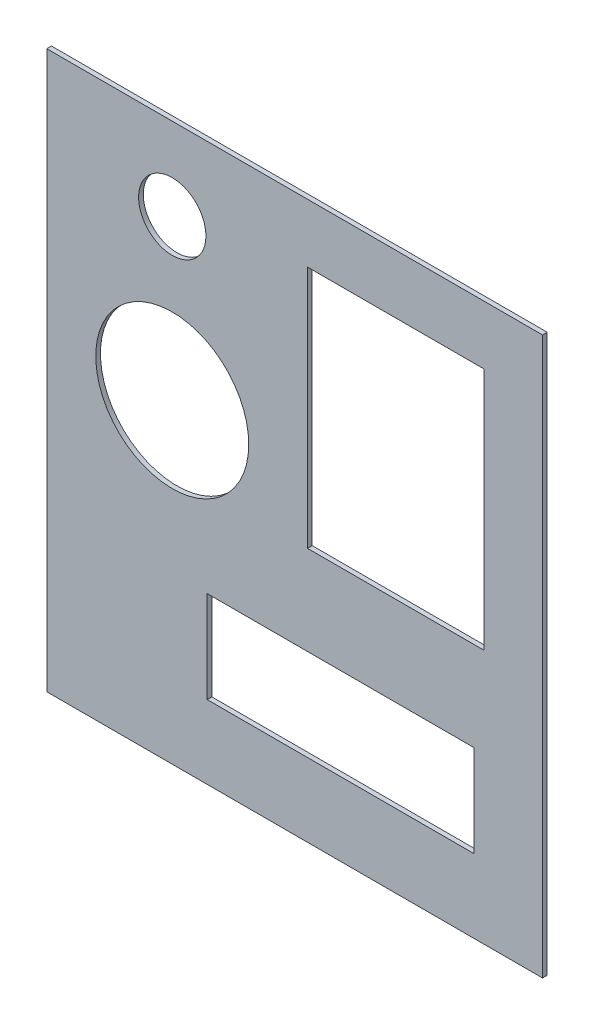
SolidWorks part; units mm, degrees
ref_plane "Front Plane" through (0, 0, 0) normal (0, 0, 1) x (1, 0, 0)
ref_plane "Top Plane" through (0, 0, 0) normal (0, 1, 0) x (1, 0, 0)
ref_plane "Right Plane" through (0, 0, 0) normal (1, 0, 0) x (0, 0, -1)
sketch "Sketch1" plane through (0, 0, 0) normal (0, 0, 1) x (1, 0, 0)
  line L1 (-64.2937, -72.2313) -> (64.2938, -72.2313)
  line L2 (-64.2937, -72.2313) -> (-64.2937, 72.2313)
  line L3 (-64.2937, 72.2313) -> (64.2938, 72.2313)
  line L4 (64.2938, -72.2313) -> (64.2938, 72.2313)
  line L5 (-64.2937, -72.2313) -> (64.2938, 72.2313) construction
  line L6 (-64.2937, 72.2313) -> (64.2938, -72.2313) construction
  point P0 (0, 0)
  dimension "D1" = 128.5875
  dimension "D2" = 144.4625
extrude "Boss-Extrude1" add sketch "Sketch1" along normal blind 1.2141 contours L3 L4 L1 L2
sketch "Sketch3" plane through (0, 0, 1.2141) normal (0, 0, 1) x (1, 0, 0)
  line L0 (-64.2937, 72.2313) -> (64.2938, 72.2313) construction
  line L1 (-27.7812, -59.5312) -> (51.5938, -59.5312)
  line L2 (-27.7812, -59.5312) -> (-27.7812, -23.0187)
  line L3 (-27.7812, -23.0187) -> (51.5938, -23.0187)
  line L4 (51.5938, -59.5312) -> (51.5938, -23.0187)
  line L5 (-27.7812, -59.5312) -> (51.5938, -23.0187) construction
  line L6 (-27.7812, -23.0187) -> (51.5938, -59.5312) construction
  line L7 (0.7938, -8.7313) -> (51.5938, -8.7313)
  line L8 (0.7938, -8.7313) -> (0.7938, 59.5312)
  line L9 (0.7938, 59.5312) -> (51.5938, 59.5312)
  line L10 (51.5938, -8.7313) -> (51.5938, 59.5312)
  line L11 (0.7938, -8.7313) -> (51.5938, 59.5312) construction
  line L12 (0.7938, 59.5312) -> (51.5938, -8.7313) construction
  line L13 (-64.2937, -72.2313) -> (64.2938, -72.2313) construction
  line L14 (64.2938, -72.2313) -> (64.2938, 72.2313) construction
  circle A0 centre (-31.75, 50.8) radius 8.7313
  circle A1 centre (-31.75, 9.525) radius 19.8438
  point P4 (11.9063, -41.275)
  point P9 (26.1938, 25.4)
  dimension "D1" = 79.375
  dimension "D5" = 17.4625
  dimension "D6" = 39.6875
  dimension "D11" = 32.5437
  dimension "D2" = 36.5125
  dimension "D3" = 50.8
  dimension "D4" = 68.2625
  dimension "D7" = 12.7
  dimension "D8" = 12.7
  dimension "D9" = 12.7
  dimension "D10" = 12.7
  dimension "D12" = 41.275
  dimension "D13" = 32.5437
extrude "Cut-Extrude1" cut sketch "Sketch3" against normal through all
sketch "Sketch4" plane through (0, 0, 1.2141) normal (0, 0, 1) x (1, 0, 0)
  line L10 (0.7938, -8.7313) -> (51.5938, -8.7313) construction
  line L11 (51.5938, -8.7313) -> (51.5938, 59.5312) construction
  line L12 (51.5938, 59.5312) -> (0.7938, 59.5312) construction
  line L13 (0.7938, 59.5312) -> (0.7938, -8.7313) construction
  line L14 (3.3338, -6.1913) -> (49.0538, -6.1913)
  line L15 (49.0538, -6.1913) -> (49.0538, 56.9912)
  line L16 (3.3338, 56.9912) -> (3.3338, -6.1913)
  line L17 (49.0538, 56.9912) -> (3.3338, 56.9912)
  line L18 (3.3338, -6.1913) -> (49.0538, -6.1913)
  line L19 (49.0538, -6.1913) -> (49.0538, 56.9912)
  line L20 (3.3338, 56.9912) -> (3.3338, -6.1913)
  line L21 (49.0538, 56.9912) -> (3.3338, 56.9912)
  line L22 (0.7938, -8.7313) -> (51.5938, -8.7313)
  line L23 (51.5938, -8.7313) -> (51.5938, 59.5312)
  line L24 (51.5938, 59.5312) -> (0.7938, 59.5312)
  line L25 (0.7938, 59.5312) -> (0.7938, -8.7313)
  dimension "D1" = 2.54
extrude "Boss-Extrude2" add sketch "Sketch4" against normal up to surface (1.2141 mm away) up to face at (-11.9062, 9.525, 0)
sketch "Sketch5" plane through (0, 0, 1.2141) normal (0, 0, 1) x (1, 0, 0)
  line L0 (51.5938, -59.5312) -> (51.5938, -23.0187) construction
  line L1 (-27.7812, -59.5312) -> (51.5938, -59.5312) construction
  line L2 (-27.7812, -23.0187) -> (-27.7812, -59.5312) construction
  line L3 (51.5938, -23.0187) -> (-27.7812, -23.0187) construction
  line L4 (51.5938, -59.5312) -> (51.5938, -23.0187)
  line L5 (-27.7812, -59.5312) -> (51.5938, -59.5312)
  line L6 (-27.7812, -23.0187) -> (-27.7812, -59.5312)
  line L7 (51.5938, -23.0187) -> (-27.7812, -23.0187)
  line L8 (46.5138, -29.3687) -> (-22.7012, -29.3687)
  line L9 (-22.7012, -53.1812) -> (46.5138, -53.1812)
  line L10 (-22.7012, -29.3687) -> (-22.7012, -53.1812)
  line L11 (46.5138, -53.1812) -> (46.5138, -29.3687)
  line L12 (-22.7012, -23.0187) -> (-22.7012, -59.5312) construction
  line L13 (51.5938, -29.3687) -> (-27.7812, -29.3687) construction
  line L14 (-27.7812, -53.1812) -> (51.5938, -53.1812) construction
  line L15 (46.5138, -59.5312) -> (46.5138, -23.0187) construction
  dimension "D1" = 6.35
  dimension "D2" = 5.08
extrude "Boss-Extrude3" add sketch "Sketch5" against normal up to surface (1.2141 mm away) up to face at (-11.9062, 9.525, 0)
